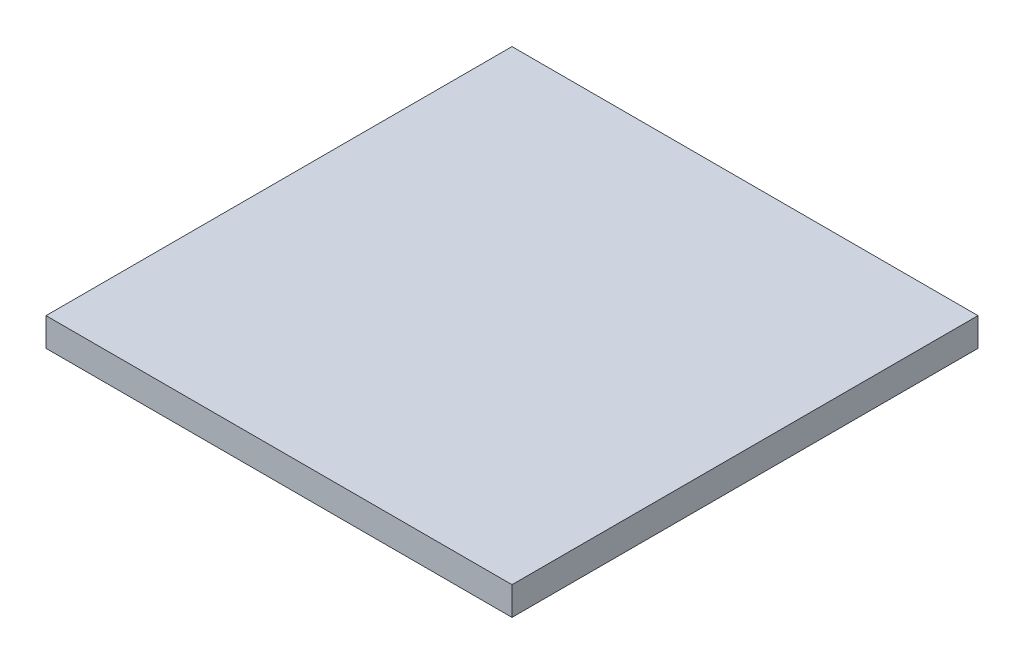
SolidWorks part; units mm, degrees
material "Sztywna pianka poliuretanowa"
ref_plane "Płaszczyzna przednia" through (0, 0, 0) normal (0, 0, 1) x (1, 0, 0)
ref_plane "Płaszczyzna górna" through (0, 0, 0) normal (0, 1, 0) x (1, 0, 0)
ref_plane "Płaszczyzna prawa" through (0, 0, 0) normal (1, 0, 0) x (0, 0, -1)
sketch "Szkic1" plane through (0, 0, 0) normal (0, 1, 0) x (1, 0, 0)
  line L1 (0, 0) -> (345, 0)
  line L2 (0, 0) -> (0, -345)
  line L3 (0, -345) -> (345, -345)
  line L4 (345, 0) -> (345, -345)
  dimension "D1" = 345
  dimension "D2" = 345
extrude "Dodanie-wyciągnięcie1" add sketch "Szkic1" along normal blind 21
